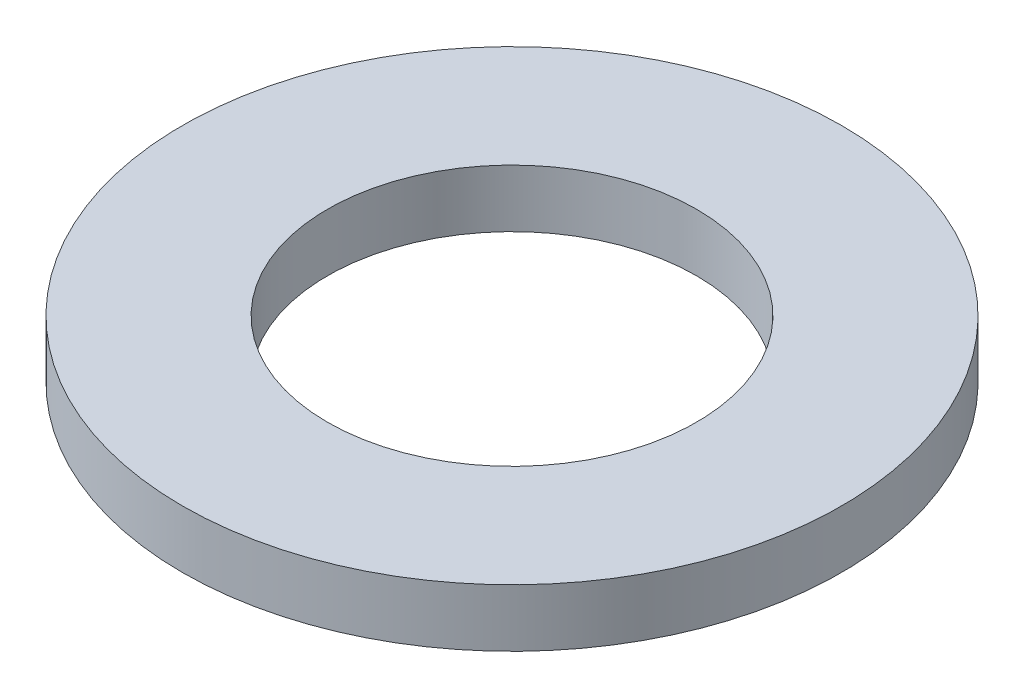
SolidWorks part; units mm, degrees
ref_plane "Front Plane" through (0, 0, 0) normal (0, 0, 1) x (1, 0, 0)
ref_plane "Top Plane" through (0, 0, 0) normal (0, 1, 0) x (1, 0, 0)
ref_plane "Right Plane" through (0, 0, 0) normal (1, 0, 0) x (0, 0, -1)
sketch "Sketch1" plane through (0, 0, 0) normal (0, 1, 0) x (1, 0, 0)
  circle A0 centre (0, 0) radius 28.575
extrude "Boss-Extrude1" add sketch "Sketch1" along normal blind 5
sketch "Sketch2" plane through (0, 5, 0) normal (0, 1, 0) x (1, 0, 0)
  circle A0 centre (0, 0) radius 16
extrude "Cut-Extrude1" cut sketch "Sketch2" against normal blind 5
